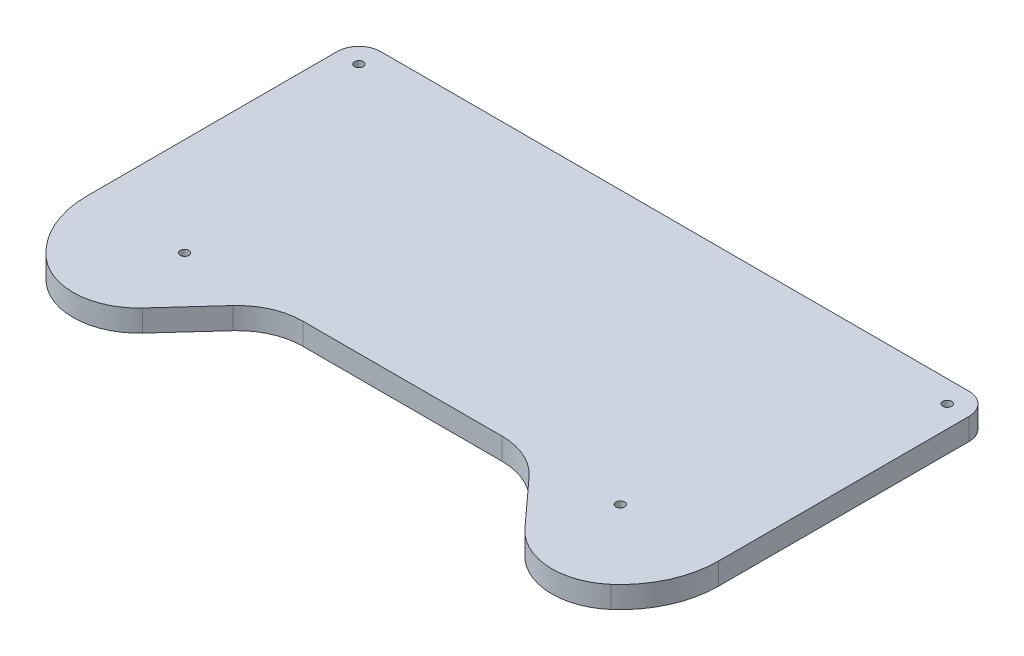
SolidWorks part; units mm, degrees
material "Acrylique (impact moyen-haut)"
ref_plane "Plan de face" through (0, 0, 0) normal (0, 0, 1) x (1, 0, 0)
ref_plane "Plan de dessus" through (0, 0, 0) normal (0, 1, 0) x (1, 0, 0)
ref_plane "Plan de droite" through (0, 0, 0) normal (1, 0, 0) x (0, 0, -1)
sketch "Esquisse2" plane through (0, 0, 0) normal (0, 1, 0) x (1, 0, 0)
  line L0 (145, 290) -> (145, 0) construction
  line L1 (0, 0) -> (290, 0)
  line L2 (0, 0) -> (0, 184.53)
  line L3 (0, 184.53) -> (290, 184.53)
  line L4 (290, 0) -> (290, 184.53)
  point P16 (145, 90)
  dimension "D2" = 290
extrude "Boss.-Extru.1" add sketch "Esquisse2" along normal blind 10
sketch "Esquisse9" plane through (0, 10, 0) normal (0, 1, 0) x (1, 0, 0)
  line L0 (145, 0) -> (145, 146.3019) construction
  line L1 (0, 0) -> (290, 0) construction
  line L2 (0, 184.53) -> (0, 0) construction
  circle A0 centre (45, 50) radius 2
  circle A1 centre (245, 50) radius 2
  dimension "D1" = 4
  dimension "D2" = 45
  dimension "D3" = 50
extrude "Enlèv. mat.-Extru.7" cut sketch "Esquisse9" against normal blind 10
sketch "Esquisse12" plane through (0, 0, 0) normal (0, -1, 0) x (1, 0, 0)
  circle A0 centre (10, -165) radius 2
  circle A1 centre (280, -165) radius 2
extrude "Enlèv. mat.-Extru.10" cut sketch "Esquisse12" against normal blind 10
sketch "Esquisse14" plane through (0, 10, 0) normal (0, 1, 0) x (1, 0, 0)
  line L0 (45, 5) -> (245, 5)
  line L1 (10, 175) -> (280, 175)
  line L4 (0, 184.53) -> (0, 0)
  line L5 (0, 0) -> (290, 0)
  line L6 (290, 0) -> (290, 184.53)
  line L7 (290, 184.53) -> (0, 184.53)
  line L8 (0, 184.53) -> (0, 0)
  line L9 (0, 0) -> (290, 0)
  line L10 (290, 0) -> (290, 184.53)
  line L11 (290, 184.53) -> (0, 184.53)
  arc A0 (10, 175) -> (0, 165) centre (10, 165) ccw
  arc A1 (290, 165) -> (280, 175) centre (280, 165) ccw
  arc A2 (245, 5) -> (290, 50) centre (245, 50) ccw
  arc A3 (0, 50) -> (45, 5) centre (45, 50) ccw
  line M9 (0, 184.53) -> (0, 0)
  line M10 (0, 0) -> (290, 0)
  line M11 (290, 0) -> (290, 184.53)
  line M12 (290, 184.53) -> (0, 184.53)
  dimension "D1" = 0
extrude "Enlèv. mat.-Extru.12" cut sketch "Esquisse14" against normal blind 10 contours A1 L10 A0 L1 M12 M9 | A3 A2 L0 M9 M10 M11
sketch "Esquisse15" plane through (0, 10, 0) normal (0, 1, 0) x (1, 0, 0)
  line L1 (245, 5) -> (203.9746, 50)
  line L2 (203.9746, 50) -> (86.0254, 50)
  line L3 (86.0254, 50) -> (45, 5)
  line L4 (145, 50) -> (145, 5) construction
  line L5 (45, 5) -> (245, 5) construction
  line L6 (45, 5) -> (245, 5)
  dimension "D1" = 45
extrude "Enlèv. mat.-Extru.13" cut sketch "Esquisse15" against normal blind 10
fillet "Congé1" radius 30 2 edges at (203.9746, 5, -50) (86.0254, 5, -50)
fillet "Congé2" radius 30 2 edges at (245, 5, -5) (45, 5, -5)
sketch "Esquisse16" plane through (0, 0, 0) normal (0, -1, 0) x (1, 0, 0)
  circle A0 centre (45, -50) radius 6
  circle A1 centre (245, -50) radius 6
  circle A2 centre (280, -165) radius 6
  circle A3 centre (10, -165) radius 6
  dimension "D1" = 12
extrude "Enlèv. mat.-Extru.14" cut sketch "Esquisse16" against normal blind 5
